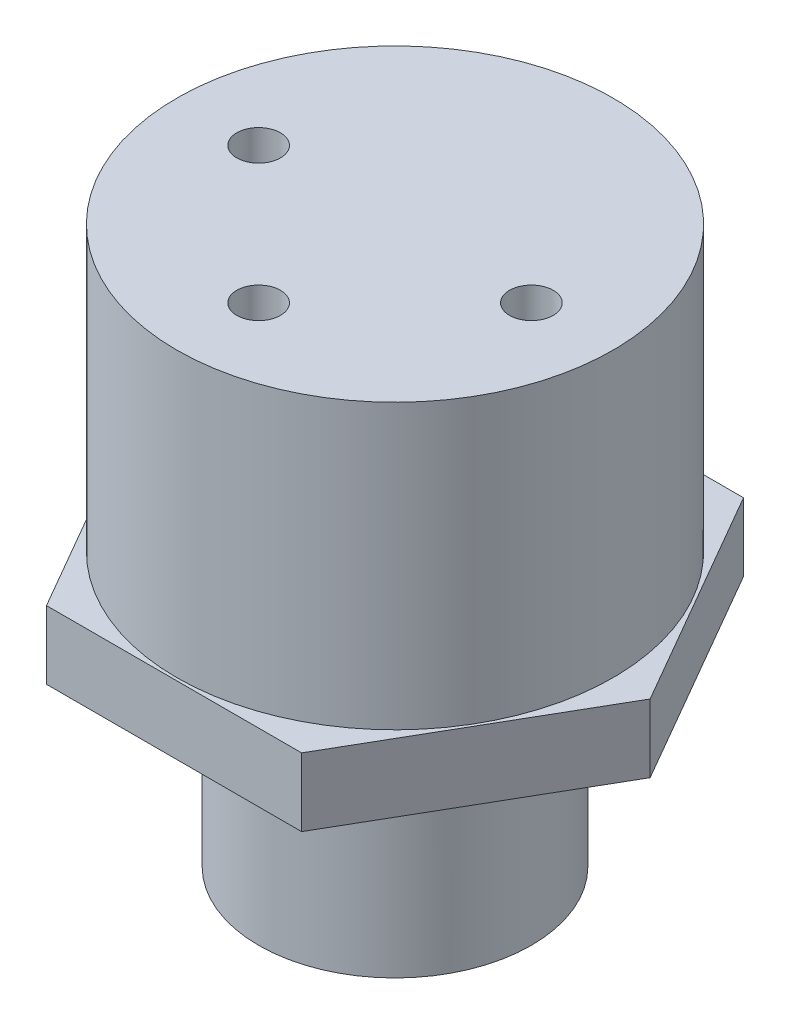
SolidWorks part; units mm, degrees
ref_plane "Front Plane" through (0, 0, 0) normal (0, 0, 1) x (1, 0, 0)
ref_plane "Top Plane" through (0, 0, 0) normal (0, 1, 0) x (1, 0, 0)
ref_plane "Right Plane" through (0, 0, 0) normal (1, 0, 0) x (0, 0, -1)
sketch "Sketch1" plane through (0, 0, 0) normal (0, 1, 0) x (1, 0, 0)
  circle A0 centre (0, 0) radius 20.32
  dimension "D1" = 40.64
extrude "Boss-Extrude1" add sketch "Sketch1" along normal blind 26.416
sketch "Sketch2" plane through (0, 0, 0) normal (0, -1, 0) x (1, 0, 0)
  line L0 (-11.8784, 20.574) -> (11.8784, 20.574)
  line L1 (11.8784, 20.574) -> (23.7568, 0)
  line L2 (23.7568, 0) -> (11.8784, -20.574)
  line L3 (11.8784, -20.574) -> (-11.8784, -20.574)
  line L4 (-11.8784, -20.574) -> (-23.7568, 0)
  line L5 (-23.7568, 0) -> (-11.8784, 20.574)
  line L6 (-23.7568, 0) -> (23.7568, 0) construction
  circle A0 centre (0, 0) radius 20.574
  point P4 (0, 0)
  dimension "D1" = 41.148
  dimension "D2" = 120
extrude "Boss-Extrude2" add sketch "Sketch2" along normal blind 6.35 contours L1 L2 L3 L4 L5 L0
sketch "Sketch3" plane through (0, -6.35, 0) normal (0, -1, 0) x (-1, 0, 0)
  circle A0 centre (0, 0) radius 12.7
  dimension "D1" = 25.4
extrude "Boss-Extrude3" add sketch "Sketch3" along normal blind 19.05
cosmetic thread "Cosmetic Thread1" parameters "D2"=23.1953
sketch "Sketch4" plane through (0, 26.416, 0) normal (0, 1, 0) x (1, 0, 0)
  line L0 (0, 0) -> (-6.5105, 0) construction
  line L1 (0, 0) -> (0, -6.0356) construction
  circle A0 centre (0, 0) radius 12.7
  circle A1 centre (0, -12.7) radius 2.032
  circle A2 centre (-12.7, 0) radius 2.032
  circle A3 centre (12.7, 0) radius 2.032
  dimension "D1" = 4.064
  dimension "D2" = 25.4
extrude "Cut-Extrude1" cut sketch "Sketch4" against normal blind 10.16
